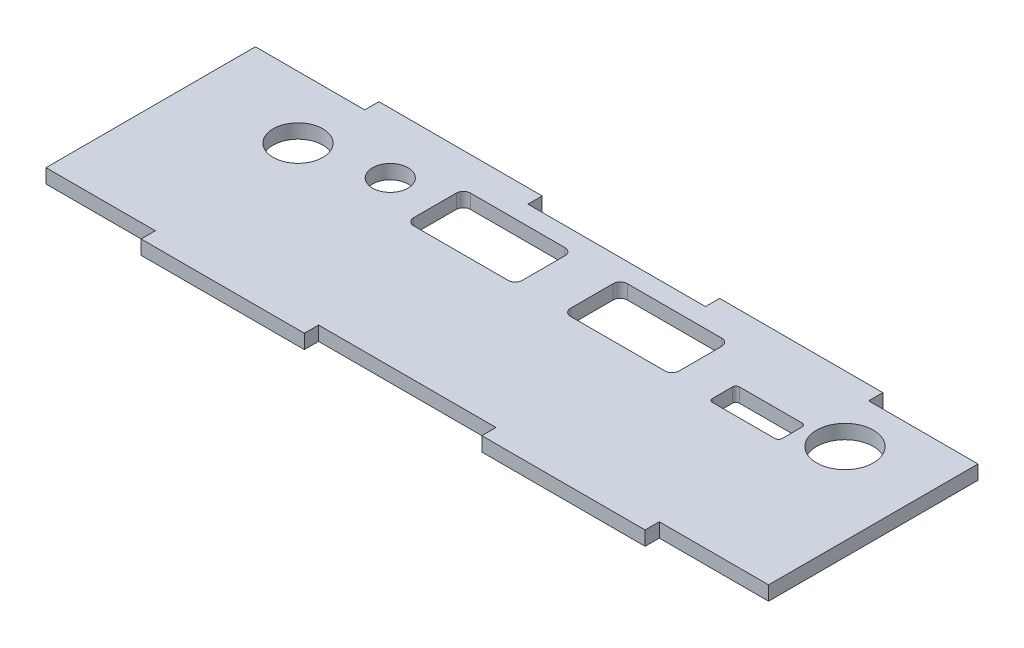
SolidWorks part; units mm, degrees
ref_plane "前视基准面" through (0, 0, 0) normal (0, 0, 1) x (1, 0, 0)
ref_plane "上视基准面" through (0, 0, 0) normal (0, 1, 0) x (1, 0, 0)
ref_plane "右视基准面" through (0, 0, 0) normal (1, 0, 0) x (0, 0, -1)
sketch "草图1" plane through (0, 0, 0) normal (0, 1, 0) x (1, 0, 0)
  line L1 (-50.9, 14.75) -> (50.9, 14.75)
  line L2 (-50.9, 14.75) -> (-50.9, -14.75)
  line L3 (-50.9, -14.75) -> (50.9, -14.75)
  line L4 (50.9, 14.75) -> (50.9, -14.75)
  line L5 (-50.9, 14.75) -> (50.9, -14.75) construction
  line L6 (-50.9, -14.75) -> (50.9, 14.75) construction
  point P0 (0, 0)
  dimension "D1" = 101.8
  dimension "D2" = 29.5
extrude "凸台-拉伸1" add sketch "草图1" along normal blind 2
sketch "草图2" plane through (0, 2, 0) normal (0, 1, 0) x (1, 0, 0)
  line L0 (50.9, 14.75) -> (-50.9, 14.75) construction
  line L1 (-35.5, 14.75) -> (-12.5, 14.75)
  line L2 (-35.5, 14.75) -> (-35.5, 16.75)
  line L3 (-35.5, 16.75) -> (-12.5, 16.75)
  line L4 (-12.5, 14.75) -> (-12.5, 16.75)
  line L5 (0, 0) -> (11.3635, 0) construction
  line L6 (12.5, 14.75) -> (35.5, 14.75)
  line L7 (12.5, 14.75) -> (12.5, 16.75)
  line L8 (12.5, 16.75) -> (35.5, 16.75)
  line L9 (35.5, 14.75) -> (35.5, 16.75)
  line L10 (35.5, -14.75) -> (35.5, -16.75)
  line L11 (12.5, -16.75) -> (35.5, -16.75)
  line L12 (12.5, -14.75) -> (12.5, -16.75)
  line L13 (12.5, -14.75) -> (35.5, -14.75)
  line L14 (-12.5, -14.75) -> (-12.5, -16.75)
  line L15 (-35.5, -16.75) -> (-12.5, -16.75)
  line L16 (-35.5, -14.75) -> (-35.5, -16.75)
  line L17 (-35.5, -14.75) -> (-12.5, -14.75)
  dimension "D1" = 23
  dimension "D2" = 23
  dimension "D3" = 12.5
  dimension "D4" = 12.5
  dimension "D5" = 2
  dimension "D6" = 2
extrude "凸台-拉伸2" add sketch "草图2" against normal blind 2
sketch "草图3" plane through (0, 2, 0) normal (0, 1, 0) x (1, 0, 0)
  line L0 (50.9, -14.75) -> (50.9, 14.75) construction
  line L1 (50.9, 14.75) -> (35.5, 14.75) construction
  circle A0 centre (39.4, 7.51) radius 4
  dimension "D2" = 8
  dimension "D1" = 11.5
  dimension "D3" = 7.24
extrude "切除-拉伸1" cut sketch "草图3" against normal through all
sketch "草图4" plane through (0, 2, 0) normal (0, 1, 0) x (1, 0, 0)
  line L0 (-35.5, 14.75) -> (-50.9, 14.75) construction
  line L1 (-50.9, 14.75) -> (-50.9, -14.75) construction
  circle A0 centre (-36.15, 6) radius 3.5
  dimension "D3" = 7
  dimension "D1" = 8.75
  dimension "D2" = 14.75
extrude "切除-拉伸2" cut sketch "草图4" against normal through all
sketch "草图5" plane through (0, 2, 0) normal (0, 1, 0) x (1, 0, 0)
  line L0 (-35.5, 14.75) -> (-50.9, 14.75) construction
  line L1 (-50.9, 14.75) -> (-50.9, -14.75) construction
  circle A0 centre (-25.4, 8.25) radius 2.5
  dimension "D3" = 5
  dimension "D1" = 6.5
  dimension "D2" = 25.5
extrude "切除-拉伸3" cut sketch "草图5" against normal through all
sketch "草图6" plane through (0, 2, 0) normal (0, 1, 0) x (1, 0, 0)
  line L0 (12.5, 14.75) -> (-12.5, 14.75) construction
  line L1 (-18.9, 12.05) -> (-3.6, 12.05)
  line L2 (-18.9, 12.05) -> (-18.9, 4.05)
  line L3 (-18.9, 4.05) -> (-3.6, 4.05)
  line L4 (-3.6, 12.05) -> (-3.6, 4.05)
  line L5 (-50.9, 14.75) -> (-50.9, -14.75) construction
  dimension "D1" = 2.7
  dimension "D2" = 8
  dimension "D3" = 32
  dimension "D4" = 15.3
extrude "切除-拉伸4" cut sketch "草图6" against normal through all
fillet "圆角1" radius 1 4 edges at (-3.6, 1, -12.05) (-3.6, 1, -4.05) (-18.9, 1, -4.05) (-18.9, 1, -12.05)
pattern_linear "阵列(线性)1" count 2 spacing 22.1 along (1, 0, 0) of "圆角1", "切除-拉伸4"
sketch "草图7" plane through (0, 2, 0) normal (0, 1, 0) x (1, 0, 0)
  line L0 (3.2, 11.05) -> (3.2, 5.05) construction
  line L1 (24.2, 7.35) -> (34, 7.35)
  line L2 (24.2, 7.35) -> (24.2, 3.55)
  line L3 (24.2, 3.55) -> (34, 3.55)
  line L4 (34, 7.35) -> (34, 3.55)
  line L6 (4.2, 4.05) -> (17.5, 4.05) construction
  dimension "D1" = 21
  dimension "D2" = 9.8
  dimension "D3" = 3.8
  dimension "D4" = 0.5
extrude "切除-拉伸5" cut sketch "草图7" against normal through all
fillet "圆角2" radius 0.5 4 edges at (34, 1, -7.35) (34, 1, -3.55) (24.2, 1, -3.55) (24.2, 1, -7.35)
